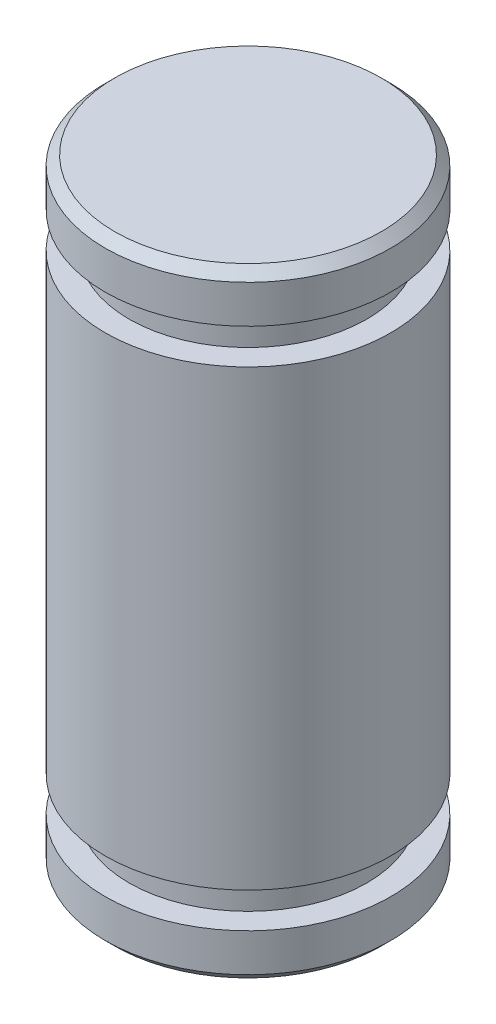
SolidWorks part; units mm, degrees
material "1060 Alloy"
ref_plane "Front Plane" through (0, 0, 0) normal (0, 0, 1) x (1, 0, 0)
ref_plane "Top Plane" through (0, 0, 0) normal (0, 1, 0) x (1, 0, 0)
ref_plane "Right Plane" through (0, 0, 0) normal (1, 0, 0) x (0, 0, -1)
sketch "Sketch1" plane through (0, 0, 0) normal (0, 0, 1) x (1, 0, 0)
  line L0 (0, 0) -> (0, 37.1759) construction
  line L2 (0, 0) -> (3, 0)
  line L3 (0, 0) -> (0, 13)
  line L4 (0, 13) -> (3, 13)
  line L5 (3, 0) -> (3, 13)
  dimension "D1" = 13
  dimension "D2" = 6
revolve "Revolve1" add sketch "Sketch1" angle 360 about L0
ref_plane "Plane1" through (0, 0, 0) normal (-1, 0, 0) x (0, 0, -1)
ref_plane "Plane2" through (0, 0, 0) normal (-1, 0, 0) x (0, 0, -1)
sketch "Sketch5" plane through (0, 0, 0) normal (-1, 0, 0) x (0, 0, -1)
  line L0 (4.55, -1.74) -> (2.5, -1.74)
  line L1 (4.55, -1.74) -> (4.55, -1)
  line L2 (4.55, -1) -> (2.5, -1)
  line L3 (2.5, -1) -> (2.5, -1.74)
  line L4 (0, -50.0288) -> (0, 49.9712) construction
  line L5 (3, 0) -> (-3, 0) construction
  line L6 (-3, -13) -> (3, -13) construction
  line L7 (2.5, -11.26) -> (4.55, -11.26)
  line L8 (2.5, -11.26) -> (2.5, -12)
  line L9 (2.5, -12) -> (4.55, -12)
  line L10 (4.55, -11.26) -> (4.55, -12)
  dimension "D1" = 2.05
  dimension "D2" = 0.74
  dimension "D3" = 1
  dimension "D4" = 2.5
  dimension "D5" = 0.74
  dimension "D6" = 1
  dimension "D7" = 2.5
  dimension "D8" = 2.05
revolve "Groove for DIN 471 - 4 x 0.4, Circlip for shafts - normal1" cut sketch "Sketch5"
chamfer "Chanfrein1" distance 0.2 angle 45 2 edges at (0, 0, -3) (0, 13, -3)
